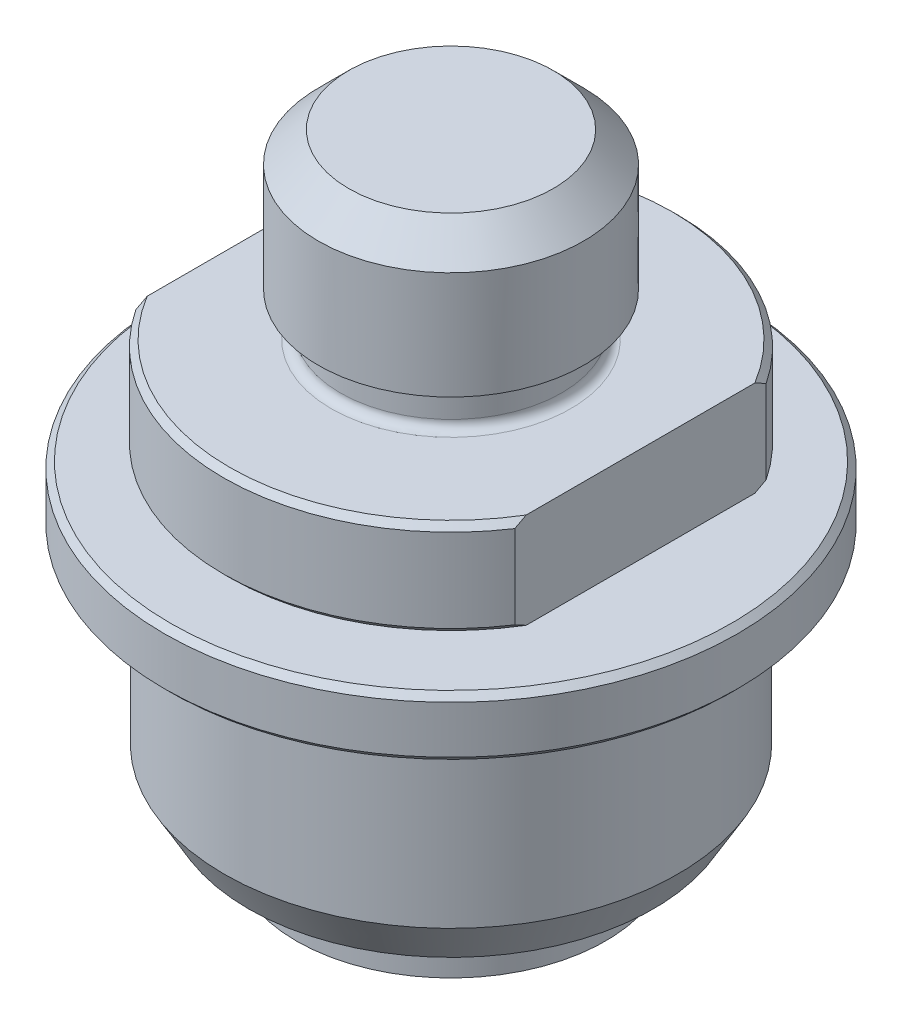
SolidWorks part; units mm, degrees
ref_plane "Front Plane" through (0, 0, 0) normal (0, 0, 1) x (1, 0, 0)
ref_plane "Top Plane" through (0, 0, 0) normal (0, 1, 0) x (1, 0, 0)
ref_plane "Right Plane" through (0, 0, 0) normal (1, 0, 0) x (0, 0, -1)
sketch "Sketch1" plane through (0, 0, 0) normal (0, 0, 1) x (1, 0, 0)
  line L0 (0, 15.24) -> (0, -21.6916)
  line L1 (0, 15.24) -> (11.1125, 15.24)
  line L2 (11.1125, 15.24) -> (11.1125, 3.683)
  line L3 (10.033, 0) -> (19.05, 0)
  line L4 (19.05, 0) -> (19.05, -8.001)
  line L5 (19.05, -8.001) -> (12.954, -8.001)
  line L6 (12.954, -8.001) -> (12.954, -33.401)
  line L7 (12.954, -37.1602) -> (10.5664, -37.1602)
  line L8 (0, 15.24) -> (0, 50.8132) construction
  line L9 (11.1125, 3.683) -> (9.271, 3.683)
  line L10 (9.271, 3.683) -> (9.271, 0.762)
  line L11 (9.0424, -35.6362) -> (9.0424, -26.035)
  line L12 (9.0424, -26.035) -> (4.699, -21.6916)
  line L13 (4.699, -21.6916) -> (0, -21.6916)
  line L14 (12.954, -35.433) -> (12.954, -37.1602)
  arc A0 (12.954, -33.401) -> (12.954, -35.433) centre (12.954, -34.417) ccw
  arc A1 (10.5664, -37.1602) -> (9.0424, -35.6362) centre (10.5664, -35.6362) cw
  arc A2 (10.033, 0) -> (9.271, 0.762) centre (10.033, 0.762) cw
  dimension "D14" = 1.016
  dimension "D15" = 1.524
  dimension "D16" = 0.762
  dimension "D1" = 22.225
  dimension "D2" = 15.24
  dimension "D3" = 8.001
  dimension "D4" = 37.1602
  dimension "D5" = 25.908
  dimension "D6" = 38.1
  dimension "D7" = 3.683
  dimension "D8" = 18.542
  dimension "D9" = 18.0848
  dimension "D10" = 11.1252
  dimension "D11" = 45
  dimension "D12" = 9.398
  dimension "D13" = 1.7272
revolve "Revolve1" add sketch "Sketch1" angle 360 about L8
chamfer "Chamfer1" distance 0.508 angle 45 2 edges at (0, -8.001, -19.05) (0, 0, -19.05)
chamfer "Chamfer2" distance 2.54 angle 45 1 edges at (0, 15.24, -11.1125)
sketch "Sketch4" plane through (0, 0, 0) normal (0, 1, 0) x (1, 0, 0)
  line L0 (-15.875, 10.5303) -> (-15.875, -10.5303)
  line L1 (15.875, 10.5303) -> (15.875, -10.5303)
  circle A0 centre (0, 0) radius 19.05 construction
  arc A1 (15.875, -10.5303) -> (15.875, 10.5303) centre (0, 0) ccw
  arc A2 (-15.875, 10.5303) -> (-15.875, -10.5303) centre (0, 0) ccw
  dimension "D1" = 15.875
  dimension "D2" = 15.875
extrude "Cut-Extrude1" cut sketch "Sketch4" against normal through all
sketch "Sketch2" plane through (0, 0, 0) normal (0, 0, 1) x (1, 0, 0)
  line L0 (13.0048, -8.8392) -> (13.0048, -29.083)
  line L1 (14.986, -32.8422) -> (16.9461, -32.8422)
  line L2 (16.9461, -32.8422) -> (18.9992, -29.2862)
  line L3 (18.9992, -29.2862) -> (18.9992, -14.605)
  line L4 (19.7612, -13.843) -> (24.003, -13.843)
  line L5 (24.003, -13.843) -> (24.003, -8.8392)
  line L6 (24.003, -8.8392) -> (13.0048, -8.8392)
  line L7 (0, 0) -> (0, 33.0062) construction
  line L8 (18.542, 0) -> (-18.542, 0) construction
  line L9 (12.954, -33.401) -> (12.954, -8.001) construction
  line L11 (14.986, -32.8422) -> (14.986, -30.099)
  line L12 (13.97, -29.083) -> (13.0048, -29.083)
  line L13 (12.954, -33.401) -> (-12.954, -33.401) construction
  line L14 (-12.954, -37.1602) -> (12.954, -37.1602) construction
  arc A0 (14.986, -30.099) -> (13.97, -29.083) centre (13.97, -30.099) ccw
  arc A1 (18.9992, -14.605) -> (19.7612, -13.843) centre (19.7612, -14.605) cw
  dimension "D13" = 1.016
  dimension "D14" = 0.762
  dimension "D1" = 24.003
  dimension "D2" = 5.0038
  dimension "D3" = 37.9984
  dimension "D4" = 48.006
  dimension "D5" = 3.556
  dimension "D6" = 30
  dimension "D7" = 33.8923
  dimension "D8" = 13.843
  dimension "D9" = 0.0508
  dimension "D10" = 4.318
  dimension "D11" = 4.318
  dimension "D12" = 29.972
revolve "Revolve2" add sketch "Sketch2" angle 360 about L7
chamfer "Chamfer3" distance 0.508 angle 45 2 edges at (0, -8.8392, -24.003) (0, -13.843, -24.003)
sketch "Sketch3" plane through (0, 0, 0) normal (0, 0, 1) x (1, 0, 0)
  line L1 (0, 0) -> (0, -31.4929) construction
  circle A0 centre (12.954, -34.417) radius 0.9652
  arc A2 (12.954, -33.401) -> (12.954, -35.433) centre (12.954, -34.417) ccw construction
  dimension "D1" = 0.0508
revolve "Revolve3" add sketch "Sketch3" angle 315 about L1
